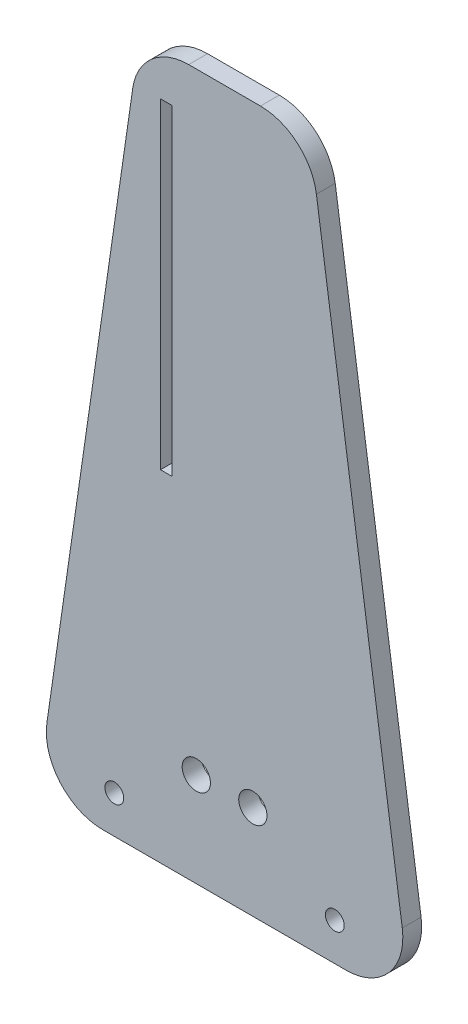
SolidWorks part; units mm, degrees
ref_plane "Front" through (0, 0, 0) normal (0, 0, 1) x (1, 0, 0)
ref_plane "Top" through (0, 0, 0) normal (0, 1, 0) x (1, 0, 0)
ref_plane "Right" through (0, 0, 0) normal (1, 0, 0) x (0, 0, -1)
sketch "草图1" plane through (0, 0, 0) normal (0, 0, 1) x (1, 0, 0)
  line L9 (-12.9172, 0) -> (12.9172, 0)
  line L16 (0, 74.8779) -> (3.8067, 74.8779)
  line L18 (0, 74.8779) -> (-3.8067, 74.8779)
  line L19 (-9.7447, 69.7383) -> (-18.8552, 6.8604)
  line L20 (9.7447, 69.7383) -> (18.8552, 6.8604)
  line L21 (-6.8, 70.2366) -> (-6.8, 36.1477)
  line L22 (-6.8, 36.1477) -> (-5.6, 36.1477)
  line L23 (-5.6, 36.1477) -> (-5.6, 70.2366)
  line L24 (-5.6, 70.2366) -> (-6.8, 70.2366)
  circle A0 centre (11.7, 4) radius 1
  circle A1 centre (-11.7, 4) radius 1
  arc A2 (12.9172, 0) -> (18.8552, 6.8604) centre (12.9172, 6) ccw
  arc A3 (-18.8552, 6.8604) -> (-12.9172, 0) centre (-12.9172, 6) ccw
  arc A4 (-9.7447, 69.7383) -> (-3.8067, 74.8779) centre (-3.8067, 68.8779) cw
  arc A5 (9.7447, 69.7383) -> (3.8067, 74.8779) centre (3.8067, 68.8779) ccw
  circle A6 centre (-3, 10) radius 1.5
  circle A7 centre (3, 10) radius 1.5
  point P0 (0, 74.8779)
  dimension "D1" = 6
  dimension "D2" = 6
  dimension "D3" = 11.7
  dimension "D4" = 4
  dimension "D5" = 4
  dimension "D6" = 6
  dimension "D7" = 11.7
  dimension "D8" = 6
  dimension "D9" = 3
  dimension "D10" = 3
  dimension "D11" = 10
  dimension "D12" = 10
extrude "凸台-拉伸1" add sketch "草图1" along normal blind 2
